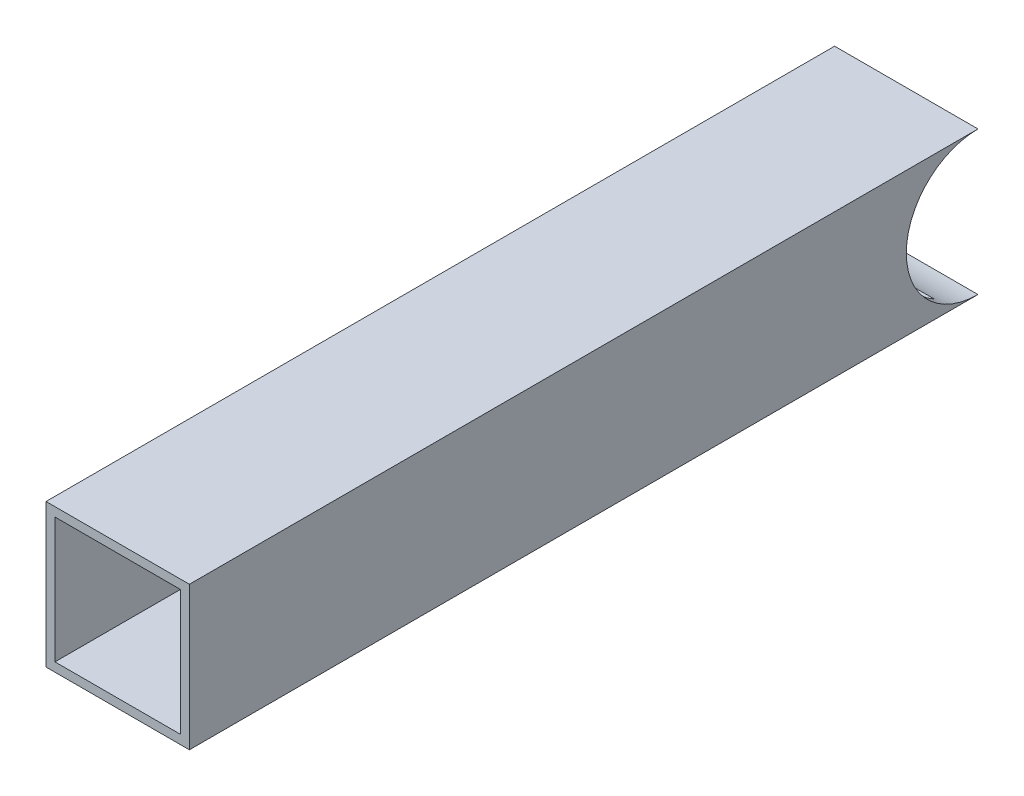
SolidWorks part; units mm, degrees
material "6061-T6 (SS)"
ref_plane "Front Plane" through (0, 0, 0) normal (0, 0, 1) x (1, 0, 0)
ref_plane "Top Plane" through (0, 0, 0) normal (0, 1, 0) x (1, 0, 0)
ref_plane "Right Plane" through (0, 0, 0) normal (1, 0, 0) x (0, 0, -1)
sketch "Sketch1" plane through (0, 0, 0) normal (0, 0, 1) x (1, 0, 0)
  line L0 (-22.225, 22.225) -> (22.225, 22.225)
  line L1 (-25.4, -25.4) -> (25.4, -25.4)
  line L2 (-25.4, -25.4) -> (-25.4, 25.4)
  line L3 (-25.4, 25.4) -> (25.4, 25.4)
  line L4 (25.4, -25.4) -> (25.4, 25.4)
  line L5 (-25.4, -25.4) -> (25.4, 25.4) construction
  line L6 (-25.4, 25.4) -> (25.4, -25.4) construction
  line L7 (22.225, -22.225) -> (22.225, 22.225)
  line L8 (-22.225, -22.225) -> (22.225, -22.225)
  line L9 (-22.225, -22.225) -> (-22.225, 22.225)
  point P0 (0, 0)
  dimension "D1" = 50.8
  dimension "D2" = 3.175
extrude "Boss-Extrude1" add sketch "Sketch1" along normal blind 279.4
sketch "Sketch2" plane through (0, 0, 0) normal (1, 0, 0) x (0, 0, -1)
  circle A0 centre (0, 0) radius 25.4
extrude "Cut-Extrude1" cut sketch "Sketch2" against normal mid plane 279.4
